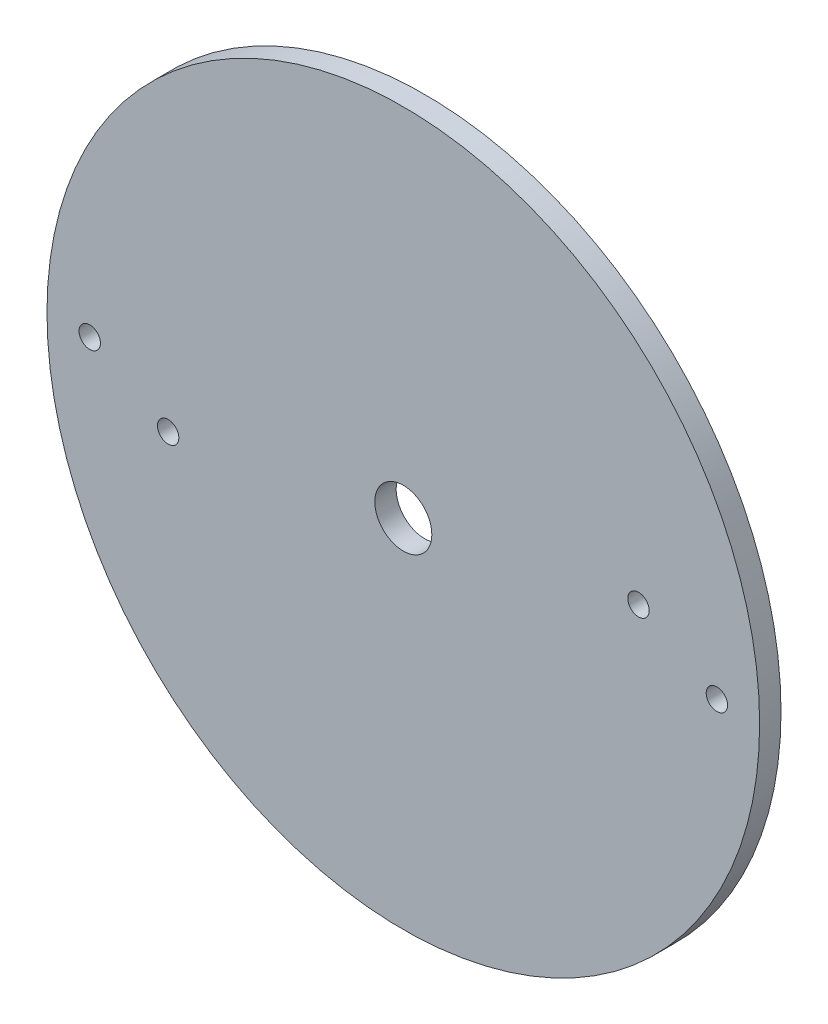
SolidWorks part; units mm, degrees
ref_plane "Plan de face" through (0, 0, 0) normal (0, 0, 1) x (1, 0, 0)
ref_plane "Plan de dessus" through (0, 0, 0) normal (0, 1, 0) x (1, 0, 0)
ref_plane "Plan de droite" through (0, 0, 0) normal (1, 0, 0) x (0, 0, -1)
sketch "Esquisse1" plane through (0, 0, 0) normal (0, 0, 1) x (1, 0, 0)
  circle A0 centre (0, 0) radius 50
  dimension "D1" = 100
extrude "Boss.-Extru.1" add sketch "Esquisse1" along normal blind 3
sketch "Esquisse2" plane through (0, 0, 3) normal (0, 0, 1) x (1, 0, 0)
  circle A0 centre (0, 0) radius 4
  dimension "D1" = 8
extrude "Enlèv. mat.-Extru.1" cut sketch "Esquisse2" against normal up to surface (3 mm away) up to face at (50, 0, 0)
sketch "Esquisse3" plane through (0, 0, 3) normal (0, 0, 1) x (1, 0, 0)
  circle A0 centre (-44, 0) radius 1.5
  circle A1 centre (0, 0) radius 50 construction
  dimension "D1" = 3
  dimension "D2" = 44
extrude "Enlèv. mat.-Extru.2" cut sketch "Esquisse3" against normal up to surface (3 mm away) up to face at (4, 0, 0)
pattern_curve "Répét. par courbe1" of "Enlèv. mat.-Extru.2" parameters "D1"=2, "D3"=10, "D2"=1, "D4"=10
sketch "Esquisse4" plane through (0, 0, 3) normal (0, 0, 1) x (1, 0, 0)
  circle A0 centre (-33, -6) radius 1.5
  circle A1 centre (-44, 0) radius 1.5 construction
  dimension "D1" = 3
  dimension "D2" = 6
  dimension "D3" = 33
extrude "Enlèv. mat.-Extru.3" cut sketch "Esquisse4" against normal up to surface (3 mm away) up to face at (45.5, 0, 0)
pattern_curve "Répét. par courbe2" of "Enlèv. mat.-Extru.3" parameters "D1"=2, "D3"=10, "D2"=1, "D4"=10
